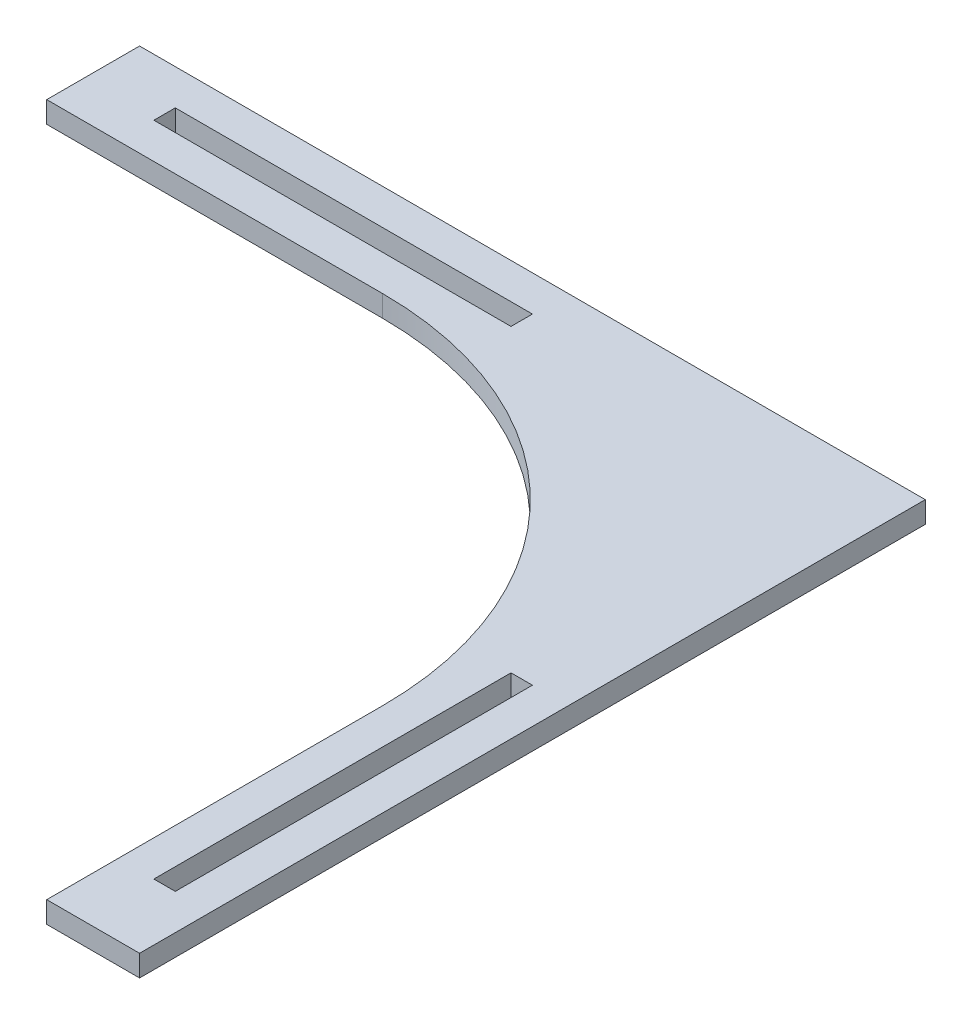
SolidWorks part; units mm, degrees
ref_plane "Front Plane" through (0, 0, 0) normal (0, 0, 1) x (1, 0, 0)
ref_plane "Top Plane" through (0, 0, 0) normal (0, 1, 0) x (1, 0, 0)
ref_plane "Right Plane" through (0, 0, 0) normal (1, 0, 0) x (0, 0, -1)
sketch "Sketch1" plane through (0, 0, 0) normal (0, 1, 0) x (1, 0, 0)
  line L0 (-55, 55) -> (-55, 63.9982) construction
  line L1 (-55, 55) -> (55, 55)
  line L2 (-55, 55) -> (-55, 42)
  line L3 (42, -55) -> (55, -55)
  line L4 (55, 55) -> (55, -55)
  line L5 (-55, 55) -> (55, -55) construction
  line L6 (-55, -55) -> (55, 55) construction
  line L8 (55, 55) -> (55, 62.4099) construction
  line L9 (55, 62.4099) -> (50, 62.4099) construction
  line L10 (-55, 42) -> (-8, 42)
  line L11 (42, -8) -> (42, -55)
  line L12 (50, 62.4099) -> (50, 72.2044) construction
  line L13 (50, 72.2044) -> (47, 72.2044) construction
  line L14 (47, 72.2044) -> (47, 80.9401) construction
  line L15 (47, 80.9401) -> (5, 80.9401) construction
  line L17 (5, 50) -> (-45, 50)
  line L18 (-45, 50) -> (-45, 47)
  line L19 (5, 47) -> (5, 50)
  line L20 (-45, 47) -> (5, 47)
  line L25 (50, 5) -> (47, 5)
  line L26 (47, 5) -> (47, -45)
  line L27 (47, -45) -> (50, -45)
  line L28 (50, -45) -> (50, 5)
  arc A0 (-8, 42) -> (42, -8) centre (-8, -8) cw
  point P0 (0, 0)
  point P21 (42, 42)
  dimension "D1" = 50
extrude "Boss-Extrude1" add sketch "Sketch1" along normal blind 3
